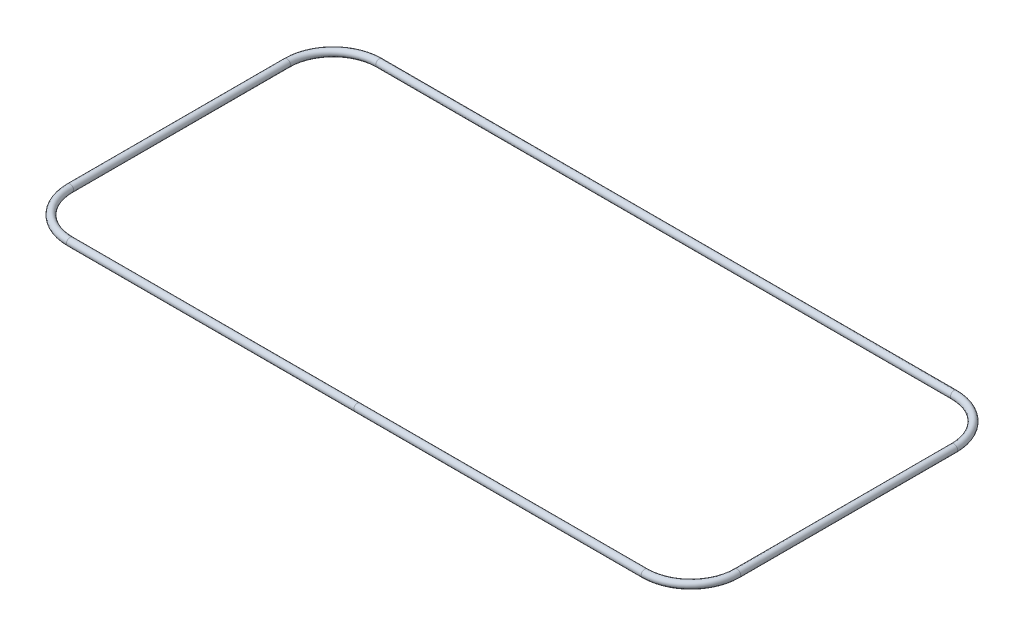
SolidWorks part; units mm, degrees
material "VITON"
ref_plane "Front Plane" through (0, 0, 0) normal (0, 0, 1) x (1, 0, 0)
ref_plane "Top Plane" through (0, 0, 0) normal (0, 1, 0) x (1, 0, 0)
ref_plane "Right Plane" through (0, 0, 0) normal (1, 0, 0) x (0, 0, -1)
sketch "Sketch1" plane through (0, 0, 0) normal (0, 1, 0) x (1, 0, 0)
  line L0 (0, 77.864) -> (0, 85.725) construction
  line L1 (-142.7991, -77.864) -> (142.7991, -77.864) construction
  line L2 (-166.764, -53.8991) -> (-166.764, 53.8991) construction
  line L3 (-142.7991, 77.864) -> (142.7991, 77.864) construction
  line L4 (166.764, -53.8991) -> (166.764, 53.8991) construction
  line L5 (-174.625, 85.725) -> (174.625, 85.725) construction
  line L6 (-174.625, 85.725) -> (-174.625, -85.725) construction
  line L7 (-174.625, -85.725) -> (174.625, -85.725) construction
  line L8 (174.625, 85.725) -> (174.625, -85.725) construction
  line L9 (0, -85.725) -> (0, -77.864) construction
  line L10 (-174.625, 0) -> (-166.764, 0) construction
  line L11 (166.764, 0) -> (174.625, 0) construction
  line L12 (-142.7991, 75.0827) -> (142.7991, 75.0827)
  line L13 (163.9827, -53.8991) -> (163.9827, 53.8991)
  line L14 (-142.7991, -75.0827) -> (142.7991, -75.0827)
  line L15 (-163.9827, -53.8991) -> (-163.9827, 53.8991)
  arc A0 (142.7991, 77.864) -> (166.764, 53.8991) centre (142.7991, 53.8991) cw construction
  arc A1 (142.7991, -77.864) -> (166.764, -53.8991) centre (142.7991, -53.8991) ccw construction
  arc A2 (-142.7991, -77.864) -> (-166.764, -53.8991) centre (-142.7991, -53.8991) cw construction
  arc A3 (-166.764, 53.8991) -> (-142.7991, 77.864) centre (-142.7991, 53.8991) cw construction
  arc A4 (142.7991, 75.0827) -> (163.9827, 53.8991) centre (142.7991, 53.8991) cw
  arc A5 (142.7991, -75.0827) -> (163.9827, -53.8991) centre (142.7991, -53.8991) ccw
  arc A6 (-142.7991, -75.0827) -> (-163.9827, -53.8991) centre (-142.7991, -53.8991) cw
  arc A7 (-163.9827, 53.8991) -> (-142.7991, 75.0827) centre (-142.7991, 53.8991) cw
  point P9 (166.764, -77.864)
  point P12 (0, 0)
  point P15 (-166.764, 77.864)
  point P20 (0, 77.864)
  point P21 (-166.764, 0)
  point P22 (-9.3366, 161.0773)
  point P23 (-10.8865, 164.0085)
  point P26 (0, 0)
  point P27 (79, 29.6504)
  point P28 (0, 0)
  point P29 (0, 0)
  point P30 (133.9503, 80.6503)
  point P31 (0, 0)
  point P32 (-145.5188, -55.6233)
  point P33 (118.4194, -60.3097)
  point P38 (0, -29.1686)
  point P39 (158.2767, 0)
  point P40 (140.157, 57.8893)
  point P236 (0, 0)
  dimension "D3" = 23.9649
  dimension "D1" = 349.25
  dimension "D2" = 171.45
  dimension "D5" = 2.7813
sketch "Sketch2" plane through (0, 0, 0) normal (1, 0, 0) x (0, 0, -1)
  circle A0 centre (-76.848, 0) radius 1.7653
  point P2 (0, 0)
  point P4 (-76.848, 0)
  point P5 (-75.0827, 0)
  dimension "D1" = 3.5306
sweep "Sweep1" add profiles "Sketch2" path "Sketch1"
equation "\"oring.277.B1\"= 11.528"
equation "\"oring.277.C\"= 11.747"
equation "\"oring.227.W\"= 0.139"
equation "\"offset\"= ( \"oring.277.C\" - \"oring.277.B1\" ) / 2"
equation "\"D3@Sketch1\"=\"offset\"+6*\"oring.227.W\""
equation "\"D4@Sketch1\"=\"oring.277.C\"*pi"
equation "\"D5@Sketch1\"=\"offset\""
equation "\"D1@Sketch2\"=\"oring.227.W\""
